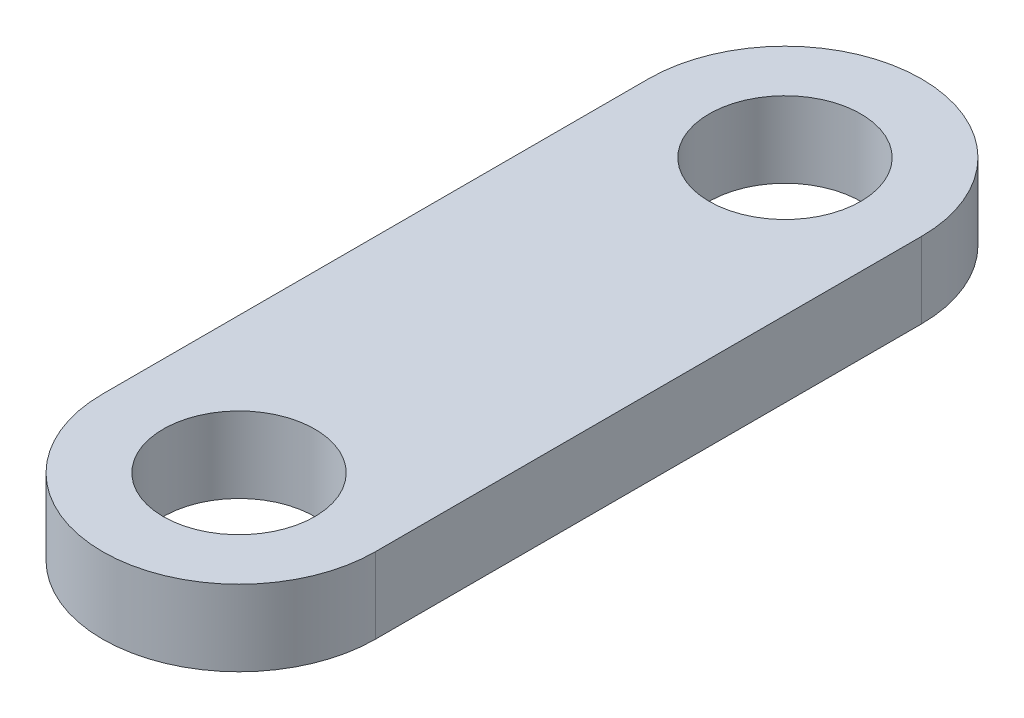
SolidWorks part; units mm, degrees
ref_plane "Front Plane" through (0, 0, 0) normal (0, 0, 1) x (1, 0, 0)
ref_plane "Top Plane" through (0, 0, 0) normal (0, 1, 0) x (1, 0, 0)
ref_plane "Right Plane" through (0, 0, 0) normal (1, 0, 0) x (0, 0, -1)
sketch "Sketch1" plane through (0, 0, 0) normal (0, 1, 0) x (1, 0, 0)
  line L0 (0, 0) -> (0, -36) construction
  line L1 (9, 0) -> (9, -36)
  line L2 (-9, 0) -> (-9, -36)
  circle A0 centre (0, 0) radius 5
  circle A1 centre (0, -36) radius 5
  arc A2 (9, 0) -> (-9, 0) centre (0, 0) ccw
  arc A3 (-9, -36) -> (9, -36) centre (0, -36) ccw
  point P5 (0, -18)
  dimension "D2" = 10
  dimension "D3" = 9
  dimension "D1" = 36
extrude "Boss-Extrude1" add sketch "Sketch1" along normal blind 5
